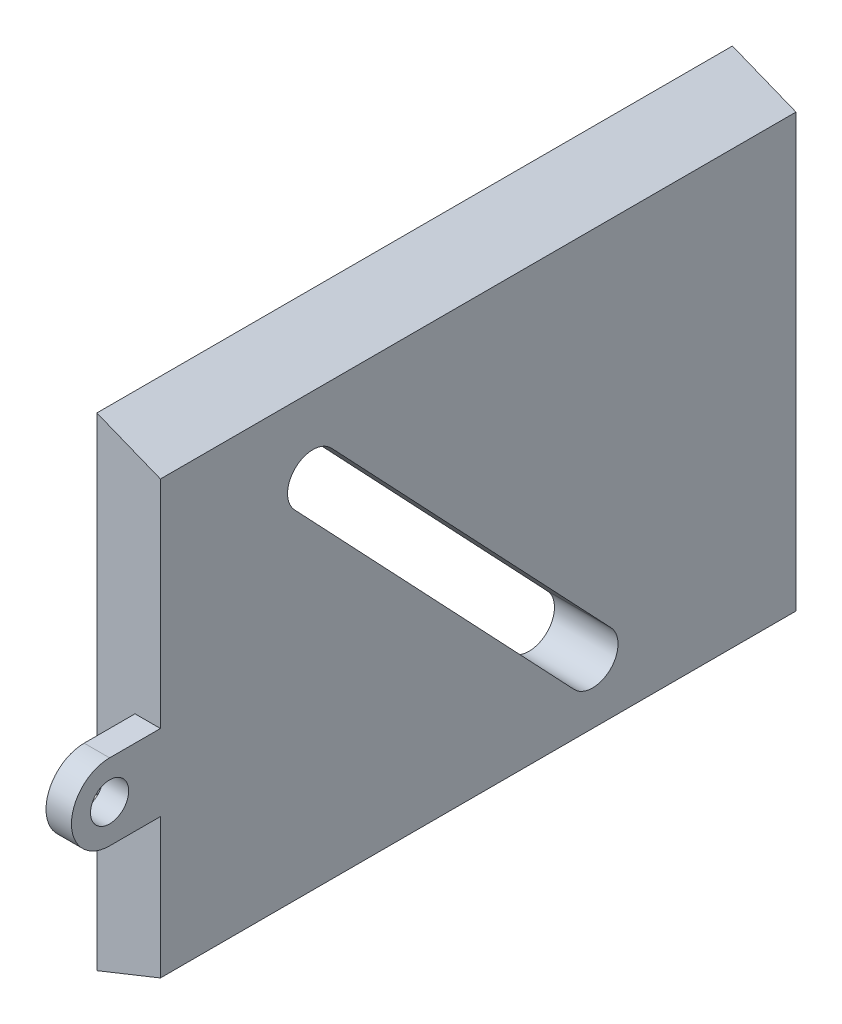
SolidWorks part; units mm, degrees
ref_plane "Front Plane" through (0, 0, 0) normal (0, 0, 1) x (1, 0, 0)
ref_plane "Top Plane" through (0, 0, 0) normal (0, 1, 0) x (1, 0, 0)
ref_plane "Right Plane" through (0, 0, 0) normal (1, 0, 0) x (0, 0, -1)
sketch "Sketch1" plane through (0, 0, 0) normal (0, 0, 1) x (1, 0, 0)
  line B0 (5, 36) -> (0, 38)
  line B1 (0, 38) -> (0, 0)
  line B2 (0, 0) -> (5, 2)
  line B3 (5, 2) -> (5, 36)
sketch_block_instance "Block1-1"
sketch_block "Block1" parameters "D1"=35, "D2"=31, "D3"=35
extrude "Boss-Extrude1" add sketch "Sketch1" along normal blind 50
sketch "Sketch2" plane through (5, 0, 0) normal (1, 0, 0) x (0, 0, -1)
  line L0 (-50, 16) -> (-54, 16) construction
  line L2 (-50, 13) -> (-54, 13)
  line L3 (-50, 19) -> (-54, 19)
  arc A0 (-50, 13) -> (-50, 19) centre (-50, 16) ccw
  arc A1 (-54, 19) -> (-54, 13) centre (-54, 16) ccw
  circle A2 centre (-54, 16) radius 1.5
  point P4 (-52, 16)
  dimension "D2" = 3
  dimension "D3" = 3
  dimension "D1" = 4
  dimension "D4" = 20
extrude "Boss-Extrude2" add sketch "Sketch2" against normal blind 2
sketch "Sketch3" plane through (5, 0, 0) normal (1, 0, 0) x (0, 0, -1)
  line L0 (-38, 30) -> (-16, 6.7621) construction
  line L1 (-36.5476, 31.375) -> (-14.5476, 8.1371)
  line L2 (-39.4524, 28.625) -> (-17.4524, 5.3871)
  line L5 (-50, 19) -> (-50, 36) construction
  line L6 (0, 2) -> (0, 36) construction
  line L7 (-50, 38) -> (0, 38) construction
  arc A0 (-36.5476, 31.375) -> (-39.4524, 28.625) centre (-38, 30) ccw
  arc A1 (-17.4524, 5.3871) -> (-14.5476, 8.1371) centre (-16, 6.7621) ccw
  point P2 (-27, 18.381)
  dimension "D1" = 2
  dimension "D2" = 8
  dimension "D3" = 12
  dimension "D4" = 16
  dimension "D5" = 32
extrude "Cut-Extrude1" cut sketch "Sketch3" against normal through all
